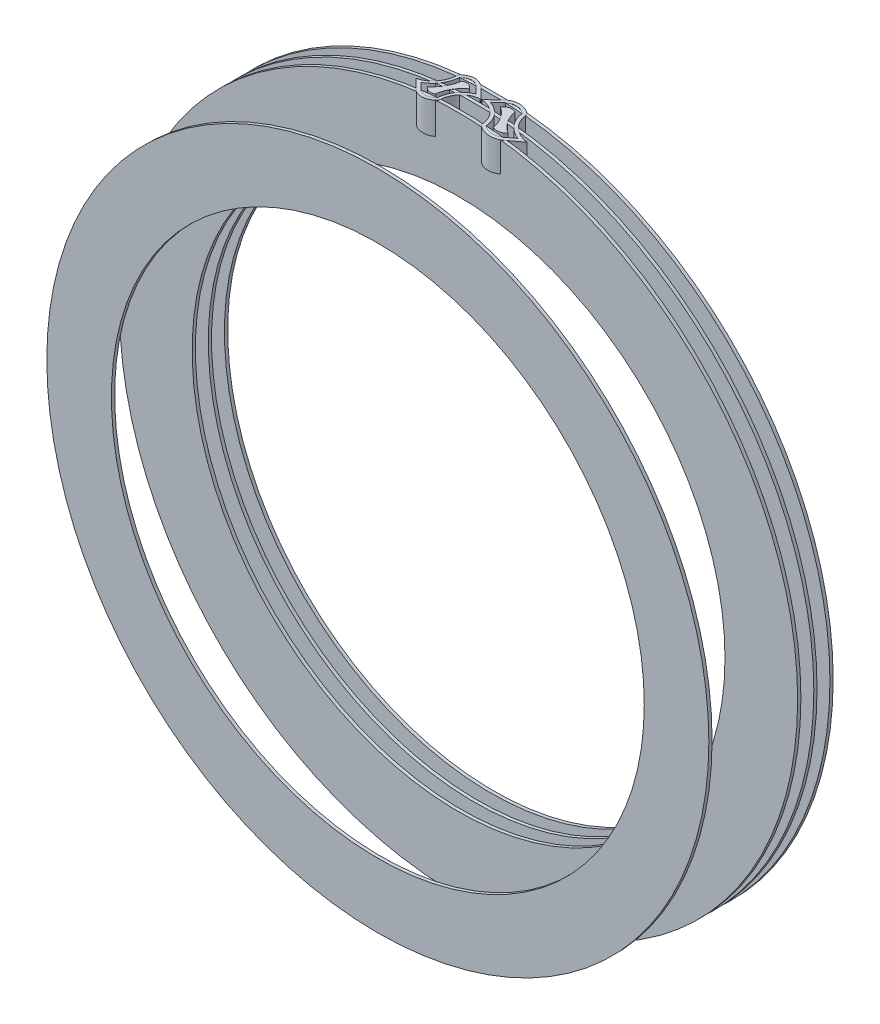
SolidWorks part; units mm, degrees
ref_plane "Front Plane" through (0, 0, 0) normal (0, 0, 1) x (1, 0, 0)
ref_plane "Top Plane" through (0, 0, 0) normal (0, 1, 0) x (1, 0, 0)
ref_plane "Right Plane" through (0, 0, 0) normal (1, 0, 0) x (0, 0, -1)
sketch "Sketch1" plane through (0, 0, 0) normal (0, 0, 1) x (1, 0, 0)
  circle A3 centre (0, 0) radius 10.4775
  circle A4 centre (0, 0) radius 13.6525
  circle A5 centre (0, 0) radius 13.0175
  circle A6 centre (0, 0) radius 12.3825
  dimension "D1" = 27.305
  dimension "D3" = 20.955
  dimension "D5" = 0.635
  dimension "D2" = 2.54
  dimension "D4" = 1.905
extrude "Boss-Extrude1" add sketch "Sketch1" along normal mid plane 0.127 contours A5 A6 | A6 A3
ref_plane "Plane1" through (0, 12.065, 0) normal (0, 1, 0) x (1, 0, 0)
sketch "Sketch3" plane through (0, 12.065, 0) normal (0, 1, 0) x (1, 0, 0)
  line L0 (0, 4.445) -> (0, 0)
  line L2 (1.5055, 3.3995) -> (1.5818, 3.4758)
  line L3 (1.3466, 4.445) -> (2.1791, 4.445)
  line L4 (0.46, 4.445) -> (0.0322, 4.0171)
  line L5 (1.73, 3.175) -> (2.1788, 3.6237)
  line L6 (1.3677, 4.318) -> (2.1791, 4.318)
  line L7 (1.857, 3.302) -> (2.179, 3.302)
  line L8 (2.179, 3.302) -> (2.179, 3.175)
  line L9 (2.179, 3.175) -> (1.73, 3.175)
  line L10 (2.1791, 4.445) -> (2.1791, 4.318)
  line L11 (1.6402, 3.2648) -> (1.9111, 3.5357)
  line L12 (0.5498, 4.3552) -> (0.279, 4.0843)
  line L13 (0.6845, 4.2205) -> (0.6083, 4.1442)
  line L14 (-0.6845, 4.2205) -> (-0.6083, 4.1442)
  line L15 (-0.5498, 4.3552) -> (-0.279, 4.0843)
  line L16 (-1.6402, 3.2648) -> (-1.9111, 3.5357)
  line L17 (-2.1791, 4.445) -> (-2.1791, 4.318)
  line L18 (-2.179, 3.175) -> (-1.73, 3.175)
  line L19 (-2.179, 3.302) -> (-2.179, 3.175)
  line L20 (-1.857, 3.302) -> (-2.179, 3.302)
  line L21 (-1.3677, 4.318) -> (-2.1791, 4.318)
  line L22 (-1.73, 3.175) -> (-2.1788, 3.6237)
  line L23 (-0.46, 4.445) -> (-0.0322, 4.0171)
  line L24 (-1.3466, 4.445) -> (-2.1791, 4.445)
  line L25 (-1.5055, 3.3995) -> (-1.5818, 3.4758)
  arc A0 (1.73, 3.175) -> (0.8763, 3.1347) centre (1.281, 3.624) cw
  arc A1 (1.3042, 4.493) -> (0.46, 4.445) centre (0.9091, 3.996) ccw
  arc A2 (0.0407, 3.9955) -> (0.8305, 3.2248) centre (0.011, 3.175) cw
  arc A3 (1.3602, 4.3824) -> (2.1788, 3.6237) centre (2.1791, 4.445) ccw
  arc A4 (0.8305, 3.2248) -> (0.8763, 3.1347) centre (0.9573, 3.2326) ccw
  arc A5 (1.3602, 4.3824) -> (1.3042, 4.493) centre (1.2328, 4.3875) ccw
  arc A6 (1.2328, 4.3875) -> (0.5498, 4.3552) centre (0.9091, 3.996) ccw
  arc A7 (-0.0322, 4.0171) -> (-0.0407, 3.9955) centre (-0.0411, 4.0081) cw
  arc A8 (1.2328, 4.3875) -> (1.9111, 3.5357) centre (2.1791, 4.445) ccw
  arc A9 (0.279, 4.0843) -> (0.9573, 3.2326) centre (0.011, 3.175) cw
  arc A10 (1.6402, 3.2648) -> (0.9573, 3.2326) centre (1.281, 3.624) cw
  arc A11 (1.0527, 4.2791) -> (0.6845, 4.2205) centre (0.9091, 3.996) ccw
  arc A12 (1.0527, 4.2791) -> (1.5818, 3.4758) centre (2.1791, 4.445) ccw
  arc A13 (0.6083, 4.1442) -> (1.1374, 3.3409) centre (0.011, 3.175) cw
  arc A14 (1.5055, 3.3995) -> (1.1374, 3.3409) centre (1.281, 3.624) cw
  arc A15 (0.0322, 4.0171) -> (0.0407, 3.9955) centre (0.0411, 4.0081) ccw
  arc A16 (-1.5055, 3.3995) -> (-1.1374, 3.3409) centre (-1.281, 3.624) ccw
  arc A17 (-0.6083, 4.1442) -> (-1.1374, 3.3409) centre (-0.011, 3.175) ccw
  arc A18 (-1.0527, 4.2791) -> (-1.5818, 3.4758) centre (-2.1791, 4.445) cw
  arc A19 (-1.0527, 4.2791) -> (-0.6845, 4.2205) centre (-0.9091, 3.996) cw
  arc A20 (-1.6402, 3.2648) -> (-0.9573, 3.2326) centre (-1.281, 3.624) ccw
  arc A21 (-0.279, 4.0843) -> (-0.9573, 3.2326) centre (-0.011, 3.175) ccw
  arc A22 (-1.2328, 4.3875) -> (-1.9111, 3.5357) centre (-2.1791, 4.445) cw
  arc A23 (-1.2328, 4.3875) -> (-0.5498, 4.3552) centre (-0.9091, 3.996) cw
  arc A24 (-1.3602, 4.3824) -> (-1.3042, 4.493) centre (-1.2328, 4.3875) cw
  arc A25 (-0.8305, 3.2248) -> (-0.8763, 3.1347) centre (-0.9573, 3.2326) cw
  arc A26 (-1.3602, 4.3824) -> (-2.1788, 3.6237) centre (-2.1791, 4.445) cw
  arc A27 (-0.0407, 3.9955) -> (-0.8305, 3.2248) centre (-0.011, 3.175) ccw
  arc A28 (-1.3042, 4.493) -> (-0.46, 4.445) centre (-0.9091, 3.996) cw
  arc A29 (-1.73, 3.175) -> (-0.8763, 3.1347) centre (-1.281, 3.624) ccw
  dimension "D1" = 0.635
extrude "Boss-Extrude3" add sketch "Sketch3" along normal offset from surface (1.2061 mm away) 0.3175 contours L4 A15 A2 A4 A0 L5 A3 A5 A1 L11 A10 A9 L12 A6 A8 | A19 A18 L25 A16 A17 L14 | L22 A29 A25 A27 A7 L23 A28 A24 A26 A22 A23 L15 A21 A20 L16 | A11 L13 A13 A14 L2 A12
ref_plane "Plane2" through (0, 0, -3.175) normal (0, 0, 1) x (1, 0, 0)
ref_plane "Plane3" through (0, 0, -3.81) normal (0, 0, 1) x (1, 0, 0)
ref_plane "Plane4" through (0, 0, -4.445) normal (0, 0, 1) x (1, 0, 0)
sketch "Sketch4" plane through (0, 0, -3.175) normal (0, 0, 1) x (1, 0, 0)
  circle A0 centre (0, 0) radius 10.4775
  circle A1 centre (0, 0) radius 13.335
extrude "Boss-Extrude4" add sketch "Sketch4" along normal mid plane 0.127
sketch "Sketch9" plane through (0, 0, -3.81) normal (0, 0, 1) x (1, 0, 0)
  circle A0 centre (0, 0) radius 10.4775
  circle A1 centre (0, 0) radius 13.335
extrude "Boss-Extrude5" add sketch "Sketch9" along normal mid plane 0.127
sketch "Sketch10" plane through (0, 0, -4.445) normal (0, 0, 1) x (1, 0, 0)
  circle A0 centre (0, 0) radius 10.4775
  circle A1 centre (0, 0) radius 13.335
extrude "Boss-Extrude6" add sketch "Sketch10" along normal mid plane 0.127
ref_plane "Plane7" through (1.905, 0, 0) normal (1, 0, 0) x (0, 0, -1)
sketch "Sketch11" plane through (1.905, 0, 0) normal (1, 0, 0) x (0, 0, -1)
  line L0 (0.0635, 12.065) -> (2.9794, 12.065) construction
  line L3 (2.582, 12.065) -> (-2.582, 12.065) construction
  line L4 (0.0635, -13.0175) -> (0.0635, 13.0175) construction
  line L5 (1.5214, 12.065) -> (1.5214, 12.077) construction
  circle A2 centre (1.5214, 12.077) radius 0.381
ref_plane "Plane8" through (0, 0, -1.651) normal (0, 0, 1) x (1, 0, 0)
sketch "Sketch12" plane through (0, 0, -1.651) normal (0, 0, 1) x (1, 0, 0)
  circle A0 centre (0, 0) radius 12.055
ref_plane "Plane9" through (0, 11.557, 0) normal (0, 1, 0) x (1, 0, 0)
